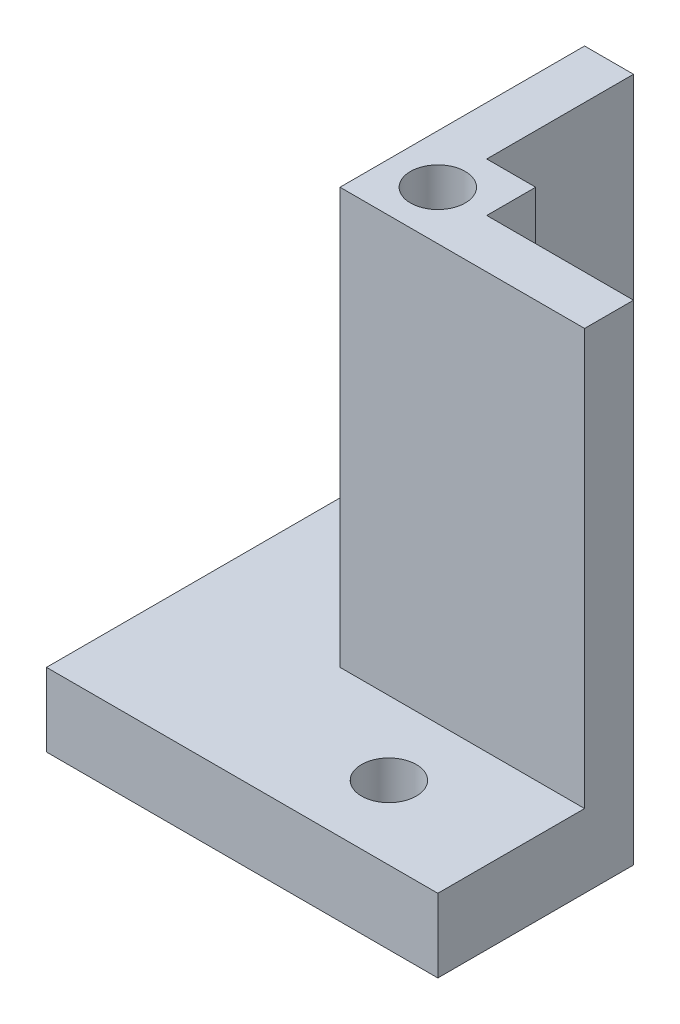
SolidWorks part; units mm, degrees
material "6061-T6 (SS)"
ref_plane "Front Plane" through (0, 0, 0) normal (0, 0, 1) x (1, 0, 0)
ref_plane "Top Plane" through (0, 0, 0) normal (0, 1, 0) x (1, 0, 0)
ref_plane "Right Plane" through (0, 0, 0) normal (1, 0, 0) x (0, 0, -1)
sketch "Sketch4" plane through (0, 0, 0) normal (0, 1, 0) x (1, 0, 0)
  line L0 (-2.7325, 2.4892) -> (-2.7325, 10.1092)
  line L5 (-2.7325, 10.1092) -> (-0.1925, 10.1092)
  line L6 (-0.1925, 10.1092) -> (-0.1925, 2.4892)
  line L8 (-2.7325, -2.5908) -> (-2.7325, 2.4892)
  line L9 (-0.1925, 2.4892) -> (2.3475, 2.4892)
  line L11 (-2.7325, -2.5908) -> (2.3475, 2.4892) construction
  line L12 (2.3475, -0.0508) -> (2.3475, 2.4892)
  line L13 (-2.7325, -2.5908) -> (2.3475, -2.5908)
  line L14 (9.9675, -0.0508) -> (2.3475, -0.0508)
  line L15 (9.9675, -2.5908) -> (9.9675, -0.0508)
  line L16 (2.3475, -2.5908) -> (9.9675, -2.5908)
  point P0 (0, 0)
  point P14 (-0.1417, 0.1417)
  dimension "D2" = 5.08
  dimension "D3" = 7.62
  dimension "D4" = 2.54
  dimension "D5" = 5.08
extrude "Boss-Extrude4" add sketch "Sketch4" along normal blind 25.4
sketch "Sketch5" plane through (0, 25.4, 0) normal (0, 1, 0) x (1, 0, 0)
  line L0 (2.3475, 2.4892) -> (-2.7325, -2.5908) construction
  circle A0 centre (-0.1925, -0.0508) radius 1.4224
  dimension "D1" = 2.8448
extrude "Cage Mounting Hole (4-40 Tapped)" cut sketch "Sketch5" against normal blind 3.81
sketch "Sketch6" plane through (0, 0, 0) normal (0, -1, 0) x (1, 0, 0)
  line L0 (9.9675, 2.5908) -> (9.9675, 10.2108)
  line L1 (9.9675, 10.2108) -> (-10.3525, 10.2108)
  line L2 (-10.3525, 10.2108) -> (-10.3525, -10.1092)
  line L3 (-10.3525, -10.1092) -> (-2.7325, -10.1092)
  line L4 (-0.1925, -10.1092) -> (-2.7325, -10.1092) construction
  line L5 (-2.7325, 2.5908) -> (-2.7325, -10.1092)
  line L6 (9.9675, 2.5908) -> (-2.7325, 2.5908)
  dimension "D1" = 7.62
  dimension "D2" = 7.62
extrude "Boss-Extrude5" add sketch "Sketch6" against normal blind 3.81
sketch "Sketch7" plane through (0, 3.81, 0) normal (0, 1, 0) x (1, 0, 0)
  line L0 (-2.7325, -2.5908) -> (-10.3525, 10.1092) construction
  line L1 (-2.7325, -2.5908) -> (9.9675, -10.2108) construction
  circle A0 centre (-6.5425, 3.7592) radius 1.4224
  circle A1 centre (3.6175, -6.4008) radius 1.4224
  circle A2 centre (-6.5425, 3.7592) radius 2.7813 construction
  dimension "D1" = 2.8448
  dimension "D2" = 2.8448
extrude "Base Mounting Holes (4-40 Clearance)" cut sketch "Sketch7" against normal blind 3.81 contours A0 | A1
equation "\"Height Needed for Telemetry\"=1"
equation "\"D1@Boss-Extrude4\"=\"Height Needed for Telemetry\""
